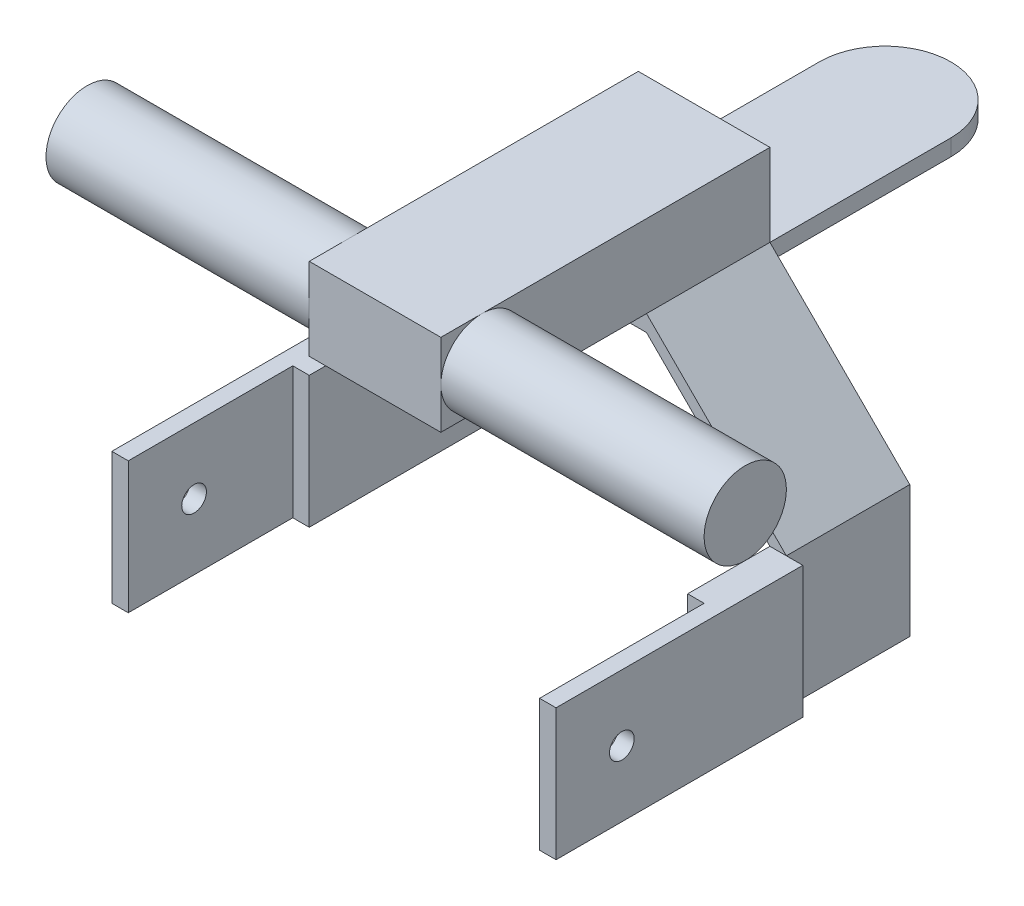
SolidWorks part; units mm, degrees
ref_plane "Front" through (0, 0, 0) normal (0, 0, 1) x (1, 0, 0)
ref_plane "Top" through (0, 0, 0) normal (0, 1, 0) x (1, 0, 0)
ref_plane "Right" through (0, 0, 0) normal (1, 0, 0) x (0, 0, -1)
sketch "草图1" plane through (0, 0, 0) normal (0, 0, 1) x (1, 0, 0)
  line L0 (-50, 16) -> (-16, 50)
  line L5 (-46, 0) -> (46, 0) construction
  line L6 (-46, 0) -> (-46, 46) construction
  line L7 (-46, 46) -> (46, 46) construction
  line L8 (46, 0) -> (46, 46) construction
  line L10 (-46, 16) -> (-46, -16)
  line L11 (-46, -16) -> (-50, -16)
  line L12 (-50, 16) -> (-50, -16)
  line L14 (46, 16) -> (46, -16)
  line L15 (46, -16) -> (50, -16)
  line L16 (50, 16) -> (50, -16)
  line L17 (-16, 46) -> (16, 46)
  line L19 (-16, 50) -> (16, 50)
  line L21 (-46, 16) -> (-16, 46)
  line L22 (46, 16) -> (16, 46)
  line L23 (50, 16) -> (16, 50)
  dimension "D1" = 92
  dimension "D2" = 46
  dimension "D3" = 46
  dimension "D4" = 32
  dimension "D5" = 16
  dimension "D6" = 4
  dimension "D7" = 32
  dimension "D8" = 4
  dimension "D9" = 16
  dimension "D10" = 32
  dimension "D11" = 4
extrude "凸台-拉伸1" add sketch "草图1" along normal blind 30
sketch "草图2" plane through (0, 0, 0) normal (0, 0, -1) x (-1, 0, 0)
  line L1 (-16, 50) -> (16, 50)
  line L2 (-16, 50) -> (-16, 46)
  line L3 (-16, 46) -> (16, 46)
  line L4 (16, 50) -> (16, 46)
extrude "凸台-拉伸2" add sketch "草图2" along normal blind 60
sketch "草图3" plane through (0, 50, 0) normal (0, 1, 0) x (1, 0, 0)
  line L2 (-16, 44) -> (-16, 67.2266)
  line L3 (-16, 67.2266) -> (16, 67.2266)
  line L4 (16, 44) -> (16, 67.2266)
  arc A0 (16, 44) -> (-16, 44) centre (0, 44) ccw
extrude "切除-拉伸1" cut sketch "草图3" against normal blind 30
sketch "草图4" plane through (-50, 0, 0) normal (-1, 0, 0) x (0, 0, 1)
  line L0 (15, 16) -> (15, -16) construction
  line L1 (30, 16) -> (0, 16) construction
  line L2 (30, -16) -> (0, -16) construction
  line L3 (0, 0) -> (30, 0) construction
  line L4 (30, 16) -> (30, -16) construction
  line L5 (10, -2) -> (10, -5)
  line L6 (10, 5) -> (20, 5)
  line L7 (10, 5) -> (10, 2)
  line L8 (10, -5) -> (20, -5)
  line L9 (20, 5) -> (20, 2)
  line L10 (10, 2) -> (20, 2)
  line L12 (10, -2) -> (20, -2)
  line L14 (20, -2) -> (20, -5)
  dimension "D1" = 10
  dimension "D2" = 5
  dimension "D3" = 10
  dimension "D4" = 5
  dimension "D5" = 2
  dimension "D6" = 2
extrude "凸台-拉伸3" add sketch "草图4" along normal blind 16
sketch "草图5" plane through (0, 5, 0) normal (0, 1, 0) x (1, 0, 0)
  line L1 (-61, -10) -> (-68.8711, -10)
  line L2 (-61, -20) -> (-61, -20.2087)
  line L3 (-61, -20.2087) -> (-68.8711, -20.2087)
  line L4 (-68.8711, -10) -> (-68.8711, -20.2087)
  arc A0 (-61, -10) -> (-61, -20) centre (-61, -15) ccw
extrude "切除-拉伸2" cut sketch "草图5" against normal blind 16
sketch "草图6" plane through (0, 0, 30) normal (0, 0, 1) x (1, 0, 0)
  line L0 (50, -16) -> (50, 16) construction
  line L1 (-50, -16) -> (-46, -16)
  line L2 (-50, -16) -> (-50, 16)
  line L3 (-50, 16) -> (-46, 16)
  line L4 (-46, -16) -> (-46, 16)
  line L5 (46, -16) -> (50, -16)
  line L6 (46, -16) -> (46, 16)
  line L7 (46, 16) -> (50, 16)
  line L8 (50, -16) -> (50, 16)
extrude "凸台-拉伸4" add sketch "草图6" along normal blind 20
sketch "草图7" plane through (0, 16, 0) normal (0, 1, 0) x (1, 0, 0)
  line L1 (-50, -30) -> (-54, -30)
  line L2 (-50, -30) -> (-50, -90)
  line L3 (-50, -90) -> (-54, -90)
  line L4 (-54, -30) -> (-54, -90)
  line L5 (50, -30) -> (54, -30)
  line L6 (50, -30) -> (50, -90)
  line L7 (50, -90) -> (54, -90)
  line L8 (54, -30) -> (54, -90)
  dimension "D1" = 60
  dimension "D2" = 4
  dimension "D3" = 4
  dimension "D4" = 60
extrude "凸台-拉伸5" add sketch "草图7" against normal blind 32
sketch "草图8" plane through (-54, 0, 0) normal (-1, 0, 0) x (0, 0, 1)
  line L0 (90, 0) -> (0, 0) construction
  line L1 (90, -16) -> (90, 16) construction
  circle A0 centre (74, 0) radius 3
  dimension "D1" = 16
extrude "切除-拉伸3" cut sketch "草图8" against normal through all
sketch "草图9" plane through (0, 50, 0) normal (0, 1, 0) x (1, 0, 0)
  line L1 (-16, 0) -> (16, 0)
  line L2 (-16, 0) -> (-16, -80)
  line L3 (-16, -80) -> (16, -80)
  line L4 (16, 0) -> (16, -80)
  dimension "D1" = 80
  dimension "D2" = 32
extrude "凸台-拉伸6" add sketch "草图9" along normal blind 20
sketch "草图10" plane through (0, 0, 0) normal (1, 0, 0) x (0, 0, -1)
  circle A0 centre (-70, 60) radius 10
extrude "凸台-拉伸7" add sketch "草图10" along normal mid plane 160
